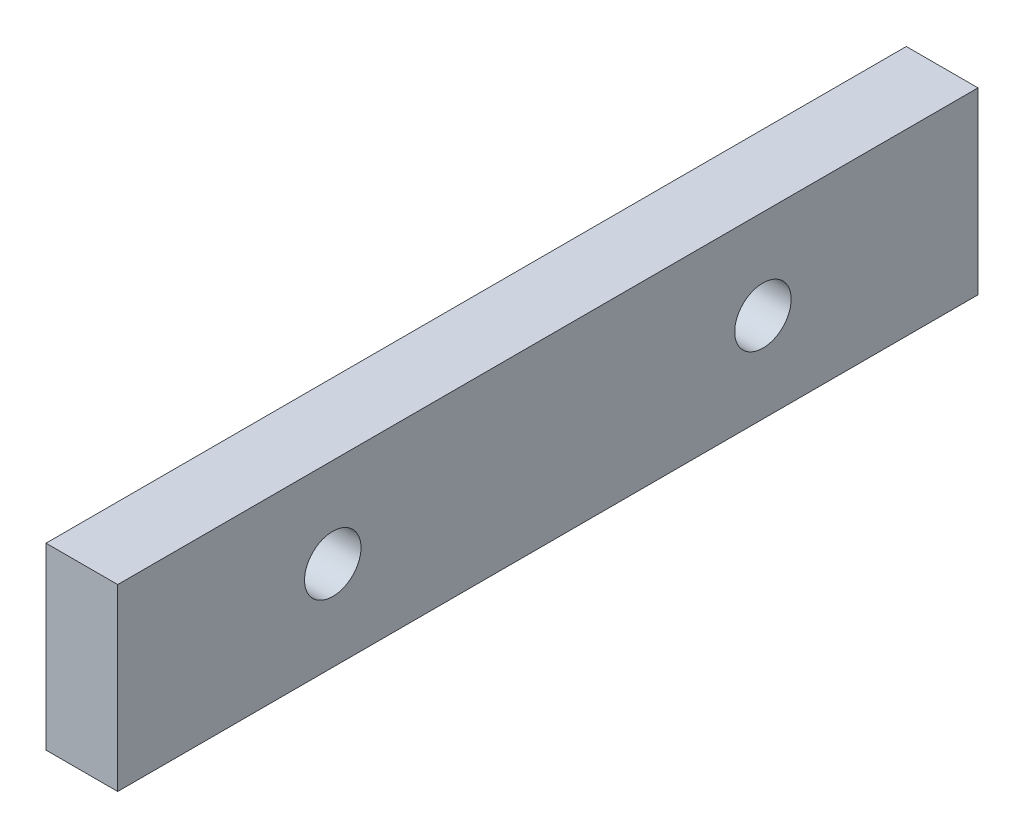
SolidWorks part; units mm, degrees
material "SS 304 (Default)"
ref_plane "Front Plane" through (0, 0, 0) normal (0, 0, 1) x (1, 0, 0)
ref_plane "Top Plane" through (0, 0, 0) normal (0, 1, 0) x (1, 0, 0)
ref_plane "Right Plane" through (0, 0, 0) normal (1, 0, 0) x (0, 0, -1)
sketch "Sketch1" plane through (0, 0, 0) normal (0, 0, 1) x (1, 0, 0)
  line L1 (-3.175, 7.9375) -> (3.175, 7.9375)
  line L2 (-3.175, 7.9375) -> (-3.175, -7.9375)
  line L3 (-3.175, -7.9375) -> (3.175, -7.9375)
  line L4 (3.175, 7.9375) -> (3.175, -7.9375)
  line L5 (-3.175, 7.9375) -> (3.175, -7.9375) construction
  line L6 (-3.175, -7.9375) -> (3.175, 7.9375) construction
  point P0 (0, 0)
  dimension "Width" = 6.35
  dimension "Height" = 15.875
extrude "Extrude1" add sketch "Sketch1" along normal mid plane 76.2
hole_wizard "M6x1.0 Tapped Hole1" positions "Sketch3" profile "Sketch2" tap size "M6x1.0" standard "Ansi Metric" end condition up to next
sketch "Sketch3" plane through (3.175, 0, 0) normal (1, 0, 0) x (0, 0, -1)
  line L0 (-19.05, 0) -> (19.05, 0) construction
  point P0 (-19.05, 0)
  point P1 (19.05, 0)
  dimension "D1" = 38.1
sketch "Sketch2" plane through (3.175, 0, 19.05) normal (0, 1, 0) x (0, 0, -1)
  line L0 (0, 0) -> (0, 6.35)
  line L1 (0, 6.35) -> (2.5, 6.35)
  line L2 (2.5, 6.35) -> (2.5, 0)
  line L5 (2.5, 0) -> (0, 0)
  line L11 (0, -6.35) -> (0, 107.95) construction
  dimension "Thru Tap Drill Dia." = 5
  dimension "Thru Tap Drill Depth" = 6.35
cosmetic thread "Hole Thread1" parameters "D2"=6
cosmetic thread "Hole Thread2" parameters "D2"=6
